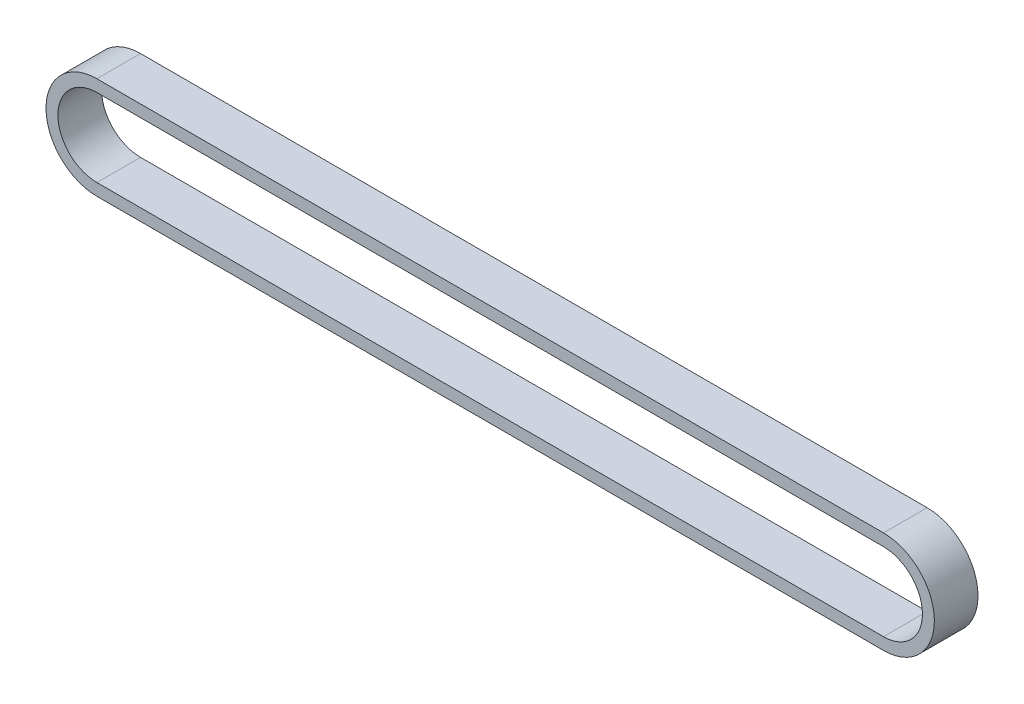
SolidWorks part; units mm, degrees
ref_plane "Front Plane" through (0, 0, 0) normal (0, 0, 1) x (1, 0, 0)
ref_plane "Top Plane" through (0, 0, 0) normal (0, 1, 0) x (1, 0, 0)
ref_plane "Right Plane" through (0, 0, 0) normal (1, 0, 0) x (0, 0, -1)
sketch "Sketch1" plane through (0, 0, 0) normal (0, 0, 1) x (1, 0, 0)
  line L0 (0, 0) -> (108.1611, 0) construction
  line L1 (0, 5.36) -> (108.1611, 5.36)
  line L2 (0, -5.36) -> (108.1611, -5.36)
  line L3 (0, 7) -> (108.1611, 7)
  line L4 (0, -7) -> (108.1611, -7)
  arc A0 (0, 5.36) -> (0, -5.36) centre (0, 0) ccw
  arc A1 (108.1611, -5.36) -> (108.1611, 5.36) centre (108.1611, 0) ccw
  arc A2 (108.1611, -7) -> (108.1611, 7) centre (108.1611, 0) ccw
  arc A3 (0, 7) -> (0, -7) centre (0, 0) ccw
  point P3 (54.0805, 0)
  dimension "D2" = 250
  dimension "D1" = 10.72
  dimension "D3" = 1.64
other "AlignGroup1"
extrude "Boss-Extrude1" add sketch "Sketch1" along normal mid plane 6
